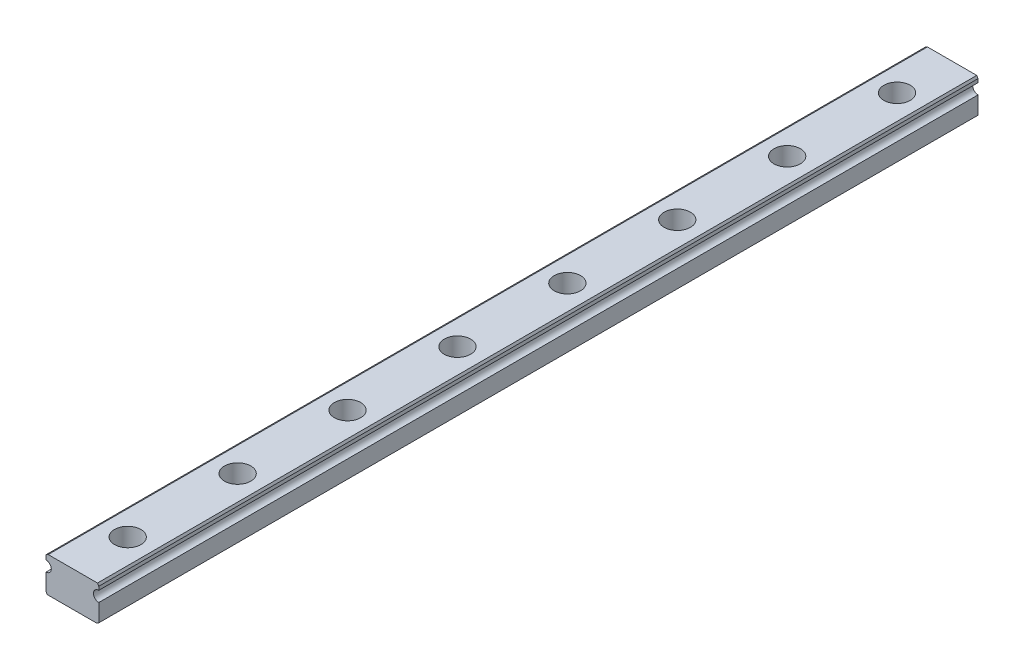
SolidWorks part; units mm, degrees
ref_plane "Front Plane" through (0, 0, 0) normal (0, 0, 1) x (1, 0, 0)
ref_plane "Top Plane" through (0, 0, 0) normal (0, 1, 0) x (1, 0, 0)
ref_plane "Right Plane" through (0, 0, 0) normal (1, 0, 0) x (0, 0, -1)
sketch "Sketch1" plane through (0, 0, 0) normal (0, 0, 1) x (1, 0, 0)
  line L0 (0, 4) -> (0, -4) construction
  line L1 (-6, -4) -> (6, -4)
  line L2 (-6, -4) -> (-6, 0.3)
  line L3 (-6, 4) -> (6, 4)
  line L4 (6, -4) -> (6, 0.3)
  line L5 (-6, -4) -> (6, 4) construction
  line L6 (-6, 4) -> (6, -4) construction
  line L7 (-6, 2.7) -> (-6, 4)
  line L8 (6, 2.7) -> (6, 4)
  arc A0 (-6, 0.3) -> (-6, 2.7) centre (-6, 1.5) ccw
  arc A1 (6, 0.3) -> (6, 2.7) centre (6, 1.5) cw
  point P0 (0, 0)
  dimension "D3" = 2.5
  dimension "D4" = 2.4
  dimension "D1" = 12
  dimension "D2" = 8
extrude "Boss-Extrude1" add sketch "Sketch1" along normal mid plane 200
chamfer "Chamfer1" distance 0.5 angle 30 4 edges at (-6, -4, 0) (6, -4, 0) (6, 4, 0) (-6, 4, 0)
sketch "Sketch2" plane through (0, 4, 0) normal (0, 1, 0) x (1, 0, 0)
  line L0 (0.1057, -100) -> (0, 0) construction
  line L1 (5.7113, -100) -> (-5.5, -100) construction
  circle A0 centre (0.0925, -87.5) radius 1.75
  dimension "D1" = 3.5
  dimension "D2" = 12.5
extrude "Cut-Extrude1" cut sketch "Sketch2" against normal up to next (8 mm away)
sketch "Sketch3" plane through (0, 4, 0) normal (0, 1, 0) x (1, 0, 0)
  circle A0 centre (0.0925, -87.5) radius 3
  dimension "D1" = 6
extrude "Cut-Extrude2" cut sketch "Sketch3" against normal blind 4.5
pattern_linear "LPattern1" count 8 spacing 25 along (0, 0, -1) of "Cut-Extrude1", "Cut-Extrude2"
